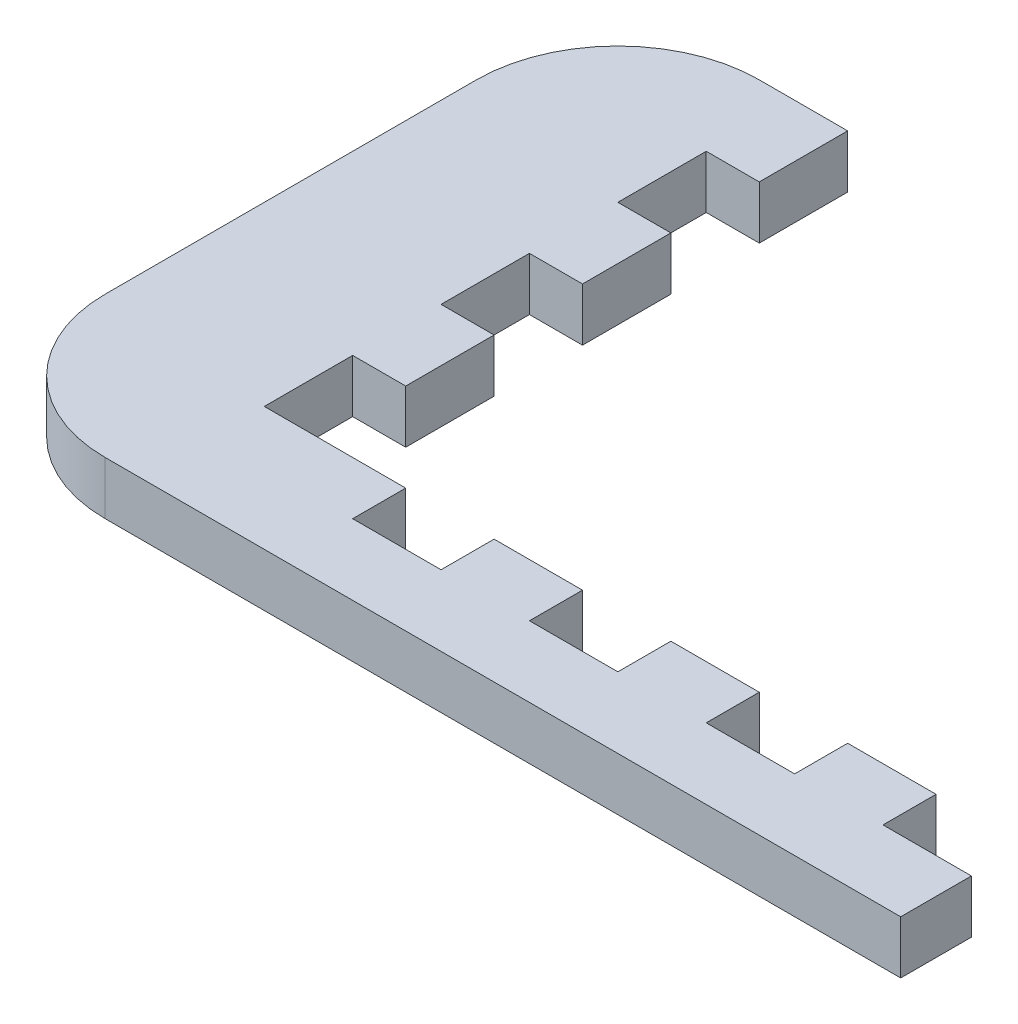
SolidWorks part; units mm, degrees
ref_plane "Front Plane" through (0, 0, 0) normal (0, 0, 1) x (1, 0, 0)
ref_plane "Top Plane" through (0, 0, 0) normal (0, 1, 0) x (1, 0, 0)
ref_plane "Right Plane" through (0, 0, 0) normal (1, 0, 0) x (0, 0, -1)
sketch "Sketch1" plane through (0, 0, 0) normal (0, 1, 0) x (1, 0, 0)
  line L1 (-24, 18.5) -> (24, 18.5)
  line L2 (-24, 18.5) -> (-24, -18.5)
  line L3 (-24, -18.5) -> (24, -18.5)
  line L4 (24, 18.5) -> (24, -18.5)
  line L5 (-24, 18.5) -> (24, -18.5) construction
  line L6 (-24, -18.5) -> (24, 18.5) construction
  point P0 (0, 0)
  dimension "D1" = 37
  dimension "D2" = 48
extrude "Boss-Extrude1" add sketch "Sketch1" along normal blind 3
sketch "Sketch3" plane through (0, 3, 0) normal (0, 1, 0) x (1, 0, 0)
  line L1 (24, 18.5) -> (-11, 18.5)
  line L2 (24, 18.5) -> (24, -11.5)
  line L3 (24, -11.5) -> (-11, -11.5)
  line L4 (-11, 18.5) -> (-11, -11.5)
  dimension "D1" = 35
  dimension "D2" = 30
extrude "Cut-Extrude1" cut sketch "Sketch3" against normal up to surface (3 mm away) up to face at (0, 0, 0)
sketch "Sketch4" plane through (0, 0, 11.5) normal (0, 0, -1) x (-1, 0, 0)
  line L0 (-24, 0) -> (11, 0) construction
  line L1 (-24, 3) -> (-19, 3)
  line L2 (-24, 3) -> (-24, 0)
  line L3 (-24, 0) -> (-19, 0)
  line L4 (-19, 3) -> (-19, 0)
  line L5 (11, 3) -> (-24, 3) construction
  line L6 (-19, 0) -> (-14, 0)
  line L7 (-19, 0) -> (-19, 3)
  line L8 (-19, 3) -> (-14, 3)
  line L9 (-14, 0) -> (-14, 3)
  line L11 (-14, 3) -> (-9, 3)
  line L12 (-14, 3) -> (-14, 0)
  line L13 (-14, 0) -> (-9, 0)
  line L14 (-9, 3) -> (-9, 0)
  line L15 (-9, 0) -> (-4, 0)
  line L16 (-9, 0) -> (-9, 3)
  line L17 (-9, 3) -> (-4, 3)
  line L18 (-4, 0) -> (-4, 3)
  line L19 (-4, 3) -> (1, 3)
  line L20 (-4, 3) -> (-4, 0)
  line L21 (-4, 0) -> (1, 0)
  line L22 (1, 3) -> (1, 0)
  line L23 (1, 0) -> (6, 0)
  line L24 (1, 0) -> (1, 3)
  line L25 (1, 3) -> (6, 3)
  line L26 (6, 0) -> (6, 3)
  line M16 (-24, 0) -> (11, 0)
  line M18 (11, 3) -> (-24, 3)
  dimension "D1" = 5
sketch "Sketch5" plane through (-11, 0, 0) normal (1, 0, 0) x (0, 0, -1)
  line L0 (-11.5, 0) -> (18.5, 0) construction
  line L1 (18.5, 3) -> (13.5, 3)
  line L2 (18.5, 3) -> (18.5, 0)
  line L3 (18.5, 0) -> (13.5, 0)
  line L4 (13.5, 3) -> (13.5, 0)
  line L5 (18.5, 3) -> (-11.5, 3) construction
  line L6 (13.5, 0) -> (8.5, 0)
  line L7 (13.5, 0) -> (13.5, 3)
  line L8 (13.5, 3) -> (8.5, 3)
  line L9 (8.5, 0) -> (8.5, 3)
  line L11 (8.5, 3) -> (3.5, 3)
  line L12 (8.5, 3) -> (8.5, 0)
  line L13 (8.5, 0) -> (3.5, 0)
  line L14 (3.5, 3) -> (3.5, 0)
  line L15 (3.5, 0) -> (-1.5, 0)
  line L16 (3.5, 0) -> (3.5, 3)
  line L17 (3.5, 3) -> (-1.5, 3)
  line L18 (-1.5, 0) -> (-1.5, 3)
  line L19 (-1.5, 3) -> (-6.5, 3)
  line L20 (-1.5, 3) -> (-1.5, 0)
  line L21 (-1.5, 0) -> (-6.5, 0)
  line L22 (-6.5, 3) -> (-6.5, 0)
  line L23 (-6.5, 0) -> (-11.5, 0)
  line L24 (-6.5, 0) -> (-6.5, 3)
  line L25 (-6.5, 3) -> (-11.5, 3)
  line L26 (-11.5, 0) -> (-11.5, 3)
  line M16 (-11.5, 0) -> (18.5, 0)
  line M18 (18.5, 3) -> (-11.5, 3)
  line M19 (-11.5, 3) -> (-11.5, 0)
  dimension "D1" = 5
extrude "Cut-Extrude2" cut sketch "Sketch5" against normal blind 3 contours L9 L4 M16 M18 | L18 L14 M16 M18 | L22 M18 M19 M16
extrude "Cut-Extrude3" cut sketch "Sketch4" against normal blind 3 contours L9 L4 M16 M18 | L18 L14 M16 M18 | L26 L22 M16 M18
sketch "Sketch6" plane through (24, 0, 0) normal (1, 0, 0) x (0, 0, -1)
  line L0 (-18.5, 0) -> (-11.5, 0) construction
  line L1 (-18.5, 3) -> (-14.5, 3)
  line L2 (-18.5, 3) -> (-18.5, 0)
  line L3 (-18.5, 0) -> (-14.5, 0)
  line L4 (-14.5, 3) -> (-14.5, 0)
  line L5 (-14.5, 0) -> (-14.5, 3) construction
extrude "Boss-Extrude2" add sketch "Sketch6" along normal blind 5
fillet "Fillet2" radius 8 2 edges at (-24, 1.5, -18.5) (-24, 1.5, 18.5)
